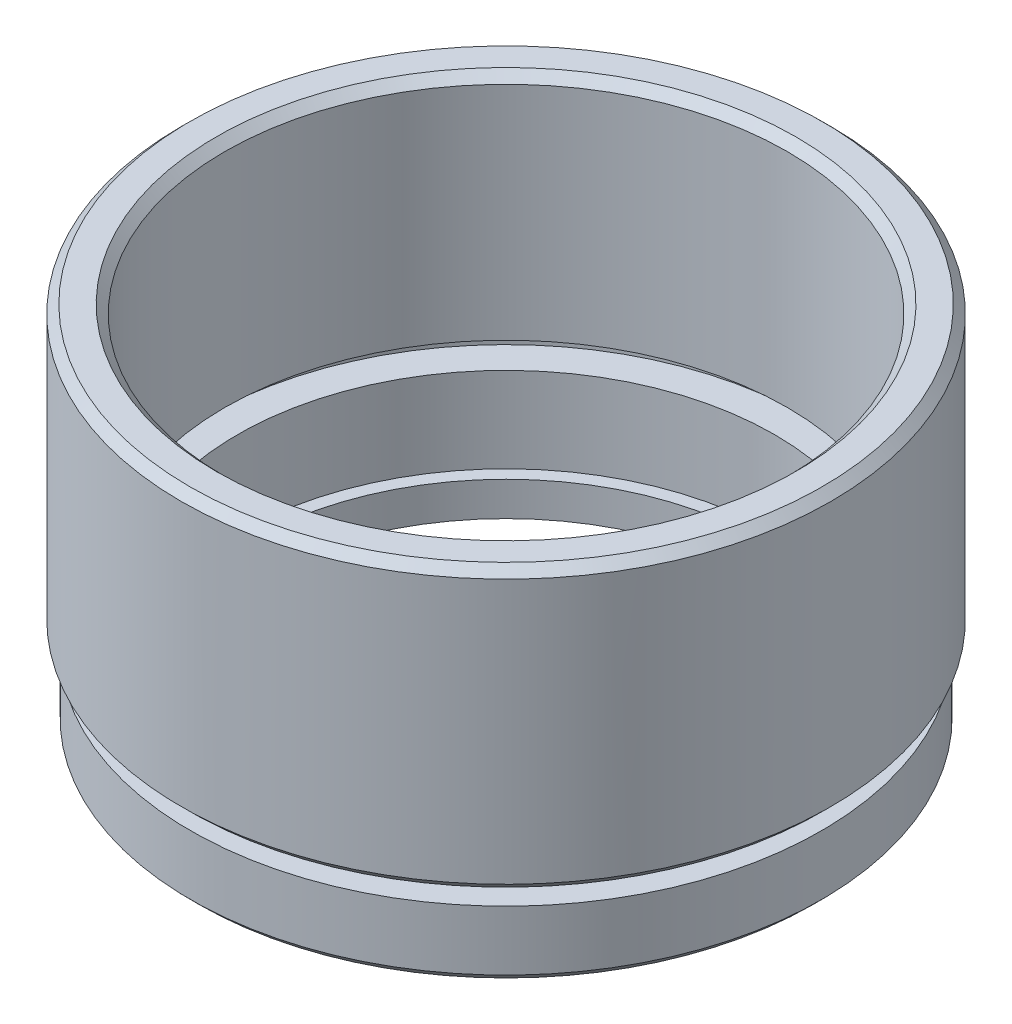
SolidWorks part; units mm, degrees
ref_plane "前视基准面" through (0, 0, 0) normal (0, 0, 1) x (1, 0, 0)
ref_plane "上视基准面" through (0, 0, 0) normal (0, 1, 0) x (1, 0, 0)
ref_plane "右视基准面" through (0, 0, 0) normal (1, 0, 0) x (0, 0, -1)
sketch "草图1" plane through (0, 0, 0) normal (0, 0, 1) x (1, 0, 0)
  line L0 (0, 0) -> (0, 21.8535) construction
  line L1 (15, 0) -> (18.5, 0)
  line L2 (18.5, 0) -> (18.5, 4)
  line L3 (18.5, 4) -> (17, 4)
  line L4 (17, 4) -> (17, 5)
  line L5 (17, 5) -> (19.05, 5)
  line L6 (19.05, 5) -> (19.05, 21.5)
  line L7 (19.05, 21.5) -> (16.5, 21.5)
  line L8 (16.5, 21.5) -> (16.5, 8)
  line L9 (16.5, 8) -> (17.6, 8)
  line L10 (17.6, 8) -> (17.6, 7)
  line L11 (17.6, 7) -> (15.75, 7)
  line L12 (15.75, 7) -> (15.75, 2)
  line L13 (15.75, 2) -> (15, 2)
  line L14 (15, 0) -> (15, 2)
  dimension "D1" = 21.5
  dimension "D2" = 19.05
  dimension "D3" = 16.5
  dimension "D4" = 15.75
  dimension "D5" = 1
  dimension "D6" = 5
  dimension "D7" = 15
  dimension "D8" = 18.5
  dimension "D9" = 1
  dimension "D10" = 5
  dimension "D11" = 2
  dimension "D12" = 17.6
  dimension "D13" = 17
revolve "旋转1" add sketch "草图1" angle 360 about L0
cosmetic thread "装饰螺纹线11" parameters "D2"=35
cosmetic thread "装饰螺纹线12" parameters "D2"=35
chamfer "倒角1" distance 0.5 angle 45 4 edges at (0, 21.5, -16.5) (0, 21.5, -19.05) (0, 5, -19.05) (0, 0, -18.5)
